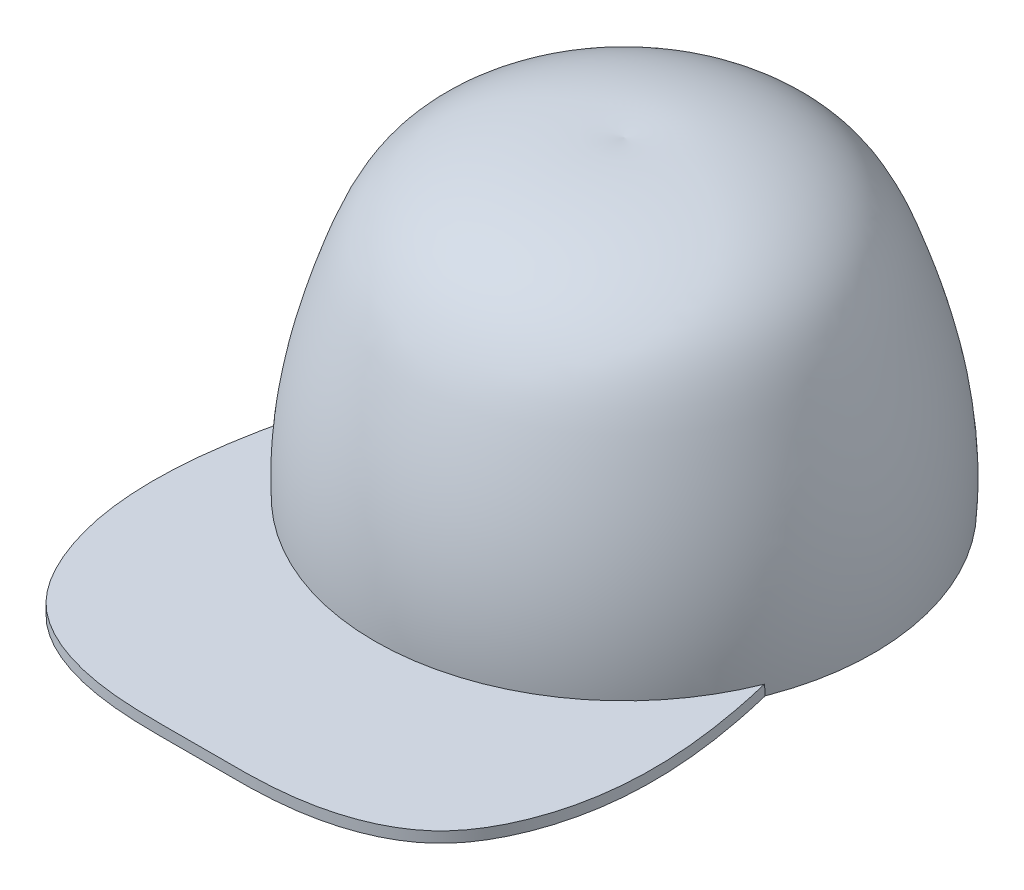
SolidWorks part; units mm, degrees
ref_plane "Front Plane" through (0, 0, 0) normal (0, 0, 1) x (1, 0, 0)
ref_plane "Top Plane" through (0, 0, 0) normal (0, 1, 0) x (1, 0, 0)
ref_plane "Right Plane" through (0, 0, 0) normal (1, 0, 0) x (0, 0, -1)
sketch "Sketch1" plane through (0, 0, 0) normal (0, 1, 0) x (1, 0, 0)
  line L0 (0, 0) -> (0, 270.85) construction
  line L1 (-90, 130.85) -> (90, 130.85) construction
  line L2 (96.5, 69.5) -> (0, 69.5) construction
  line L3 (76.5, 69.5) -> (76.5, 18.2) construction
  line L4 (36.5, 69.5) -> (36.5, 1.15) construction
  line L5 (70, 130.85) -> (70, 253.35) construction
  arc A0 (-90, 130.85) -> (90, 130.85) centre (0, 166.1897) ccw
  spline S0 degree 3 poles (90, 130.85) (96.9541, 101.6263) (102.4332, 59.8939) (68.9073, -0.1393) (23.6203, -1.1191) (0, 0) knots 0 0 0 0 0.464756 0.594997 1 1 1 1
  spline S1 degree 3 poles (-90, 130.85) (-96.9541, 101.6263) (-102.4332, 59.8939) (-68.9073, -0.1393) (-23.6203, -1.1191) (0, 0) knots 0 0 0 0 0.464756 0.594997 1 1 1 1
  spline S2 degree 2 poles (90, 130.85) (124.3948, 273.9038) (0, 270.85) knots 0 0 0 1 1 1
  spline S3 degree 2 poles (-90, 130.85) (-124.3948, 273.9038) (0, 270.85) knots 0 0 0 1 1 1
  point P3 (0, 69.5)
  point P4 (0, 130.85)
  point P7 (96.5, 69.5)
  point P8 (-96.5, 69.5)
  point P10 (90, 40.1)
  dimension "D1" = 69.5
  dimension "D2" = 130.85
  dimension "D3" = 90
  dimension "D4" = 122.5
  dimension "D5" = 140
  dimension "D6" = 96.5
  dimension "D7" = 96.5
  dimension "D8" = 90.75
  dimension "D9" = 20
  dimension "D10" = 51.3
  dimension "D11" = 60
  dimension "D12" = 68.35
  dimension "D13" = 69.5
  dimension "D14" = 20
sketch "Sketch5" plane through (0, 0, 0) normal (0, 1, 0) x (1, 0, 0)
  line L0 (0, 0) -> (0, 270.85) construction
  arc A0 (-90, 130.85) -> (90, 130.85) centre (0, 166.1715) ccw
  arc A1 (-88.1698, 131.6565) -> (88.2862, 131.881) centre (0.0144, 166.1955) ccw
  spline S0 degree 3 poles (-90, 130.85) (-97.0793, 101.6758) (-102.3198, 59.8491) (-75.2209, 11.0048) (-38.5303, -1.0698) (0, 0.4883) (38.5303, -1.0698) (75.2209, 11.0048) (102.3198, 59.8491) (97.0793, 101.6758) (90, 130.85) knots 0 0 0 0 0.232378 0.297499 0.407563 0.5 0.592437 0.702501 0.767622 1 1 1 1
  spline S1 degree 2 poles (-90, 130.85) (-124.3948, 273.9038) (0, 270.85) knots 0 0 0 1 1 1
  spline S2 degree 2 poles (-88.1698, 131.6565) (-122.168, 272.0844) (0, 268.85) knots 0 0 0 1 1 1
  spline S3 degree 2 poles (88.1698, 131.6565) (122.168, 272.0844) (0, 268.85) knots 0 0 0 1 1 1
  spline S4 degree 2 poles (90, 130.85) (124.3948, 273.9038) (0, 270.85) knots 0 0 0 1 1 1
  point P0 (-90, 130.85)
  point P1 (-96.5, 69.5)
  point P3 (-90, 40.1)
  point P5 (-76.5, 18.2)
  point P7 (-36.5, 1.15)
  point P9 (0, 0)
  point P11 (36.5, 1.15)
  point P13 (76.5, 18.2)
  point P15 (90, 40.1)
  point P17 (96.5, 69.5)
  point P19 (90, 130.85)
  point P21 (0, 69.5)
  point P28 (-70, 253.35)
  point P30 (-90, 130.85)
  point P32 (0, 270.85)
  point P34 (70, 253.35)
  point P36 (0, 268.85)
  point P38 (-68.7759, 251.7684)
  point P40 (68.4813, 252.0487)
  point P42 (88.2862, 131.881)
  point P44 (-88.1698, 131.6565)
  point P45 (0, 71.5)
  dimension "D1" = 2
  dimension "D2" = 2
  dimension "D3" = 2
  dimension "D4" = 2
  dimension "D5" = 2
  dimension "D6" = 2
sketch "Sketch7" plane through (0, 0, 0) normal (0, 1, 0) x (1, 0, 0)
  arc A0 (90, 130.85) -> (-90, 130.85) centre (0, 166.1767) cw
  spline S0 degree 3 poles (90, 130.85) (97.0793, 101.6758) (102.3198, 59.8491) (75.2209, 11.0048) (38.5303, -1.0698) (0, 0.4883) (-38.5303, -1.0698) (-75.2209, 11.0048) (-102.3198, 59.8491) (-97.0793, 101.6758) (-90, 130.85) knots 0 0 0 0 0.232378 0.297499 0.407563 0.5 0.592437 0.702501 0.767622 1 1 1 1
  point P0 (0, 0)
  point P1 (-36.5, 1.15)
  point P3 (-76.5, 18.2)
  point P5 (-90, 40.1)
  point P7 (-96.5, 69.5)
  point P9 (-90, 130.85)
  point P11 (0, 69.5)
  point P13 (90, 130.85)
  point P15 (96.5, 69.5)
  point P17 (90, 40.1)
  point P19 (76.5, 18.2)
  point P21 (36.5, 1.15)
extrude "Boss-Extrude3" add sketch "Sketch7" along normal blind 4.18
sketch "Sketch8" plane through (0, 0, 0) normal (0, -1, 0) x (-1, 0, 0)
  line L0 (0, 270.85) -> (0, -32.2535) construction
  arc A0 (88.1698, 131.6565) -> (-88.1698, 131.6565) centre (0, 166.4634) cw
  arc A1 (90, 130.85) -> (-90, 130.85) centre (0, 166.1503) cw
  spline S0 degree 2 poles (90, 130.85) (124.3948, 273.9038) (0, 270.85) knots 0 0 0 1 1 1
  spline S1 degree 2 poles (88.1698, 131.6565) (122.168, 272.0844) (0, 268.85) knots 0 0 0 1 1 1
  spline S2 degree 2 poles (-88.1698, 131.6565) (-122.168, 272.0844) (0, 268.85) knots 0 0 0 1 1 1
  spline S3 degree 2 poles (-90, 130.85) (-124.3948, 273.9038) (0, 270.85) knots 0 0 0 1 1 1
  point P0 (90, 130.85)
  point P1 (0, 69.5)
  point P3 (-90, 130.85)
  point P5 (-70, 253.35)
  point P7 (0, 270.85)
  point P9 (70, 253.35)
  point P11 (68.7759, 251.7684)
  point P13 (0, 268.85)
  point P15 (-68.4813, 252.0487)
  point P17 (-88.2862, 131.881)
  point P19 (0, 71.5)
  point P21 (88.1698, 131.6565)
sketch "Sketch9" plane through (0, 0, 0) normal (1, 0, 0) x (0, 0, -1)
  line L0 (0, 0) -> (270.85, 0) construction
  line L1 (166.18, 0) -> (166.18, 125) construction
  line L2 (166.18, 125) -> (166.18, 0)
  line L3 (166.18, 0) -> (69.5, 0)
  line L4 (166.18, 0) -> (166.18, 87.121) construction
  line L5 (166.18, 87.121) -> (166.18, 0)
  spline S0 degree 3 poles (69.5, 0) (67.5819, 26.8507) (75.089, 61.0707) (98.2638, 120.3419) (143.4984, 127.7419) (166.18, 125) knots 0 0 0 0 0.425687 0.582159 1 1 1 1
  spline S1 degree 3 poles (71.5, 0) (69.4865, 26.9773) (77.2565, 60.8484) (99.6163, 119.8609) (144.9681, 124.9589) (166.18, 123) knots 0 0 0 0 0.43212 0.590958 1 1 1 1
  point P4 (69.5, 0)
  point P5 (166.18, 0)
  point P10 (71.5, 0)
  point P12 (73.6015, 38.858)
  point P14 (83.7603, 77.0479)
  point P16 (96.5765, 102.8728)
  point P17 (124.9144, 119.4391)
  point P18 (166.18, 123)
  dimension "D1" = 69.5
  dimension "D2" = 96.68
  dimension "D3" = 125
  dimension "D4" = 2
  dimension "D5" = 2
  dimension "D6" = 2
  dimension "D7" = 2
  dimension "D8" = 2
  dimension "D9" = 2
sketch "Sketch10" plane through (0, 0, 0) normal (0, -1, 0) x (-1, 0, 0)
  line L0 (0, 69.5) -> (0, 270.85) construction
  arc A0 (-90, 130.85) -> (90, 130.85) centre (0, 166.0273) ccw
  spline S0 degree 2 poles (-90, 130.85) (-124.3948, 273.9038) (0, 270.85) knots 0 0 0 1 1 1
  spline S1 degree 2 poles (90, 130.85) (124.3948, 273.9038) (0, 270.85) knots 0 0 0 1 1 1
  point P0 (0, 69.5)
  point P1 (90, 130.85)
  point P3 (70, 253.35)
  point P5 (0, 270.85)
  point P7 (-70, 253.35)
  point P9 (-90, 130.85)
revolve "Revolve2" add sketch "Sketch9" angle 360 about L2
sketch "Sketch14" plane through (0, 4.18, 0) normal (0, 1, 0) x (1, 0, 0)
  line L0 (0, 0) -> (0, 69.26) construction
  arc A0 (-90.0956, 130.4551) -> (90.0956, 130.4551) centre (0, 166.18) ccw construction
  point P6 (0, 34.63)
sketch "Sketch15" plane through (0, 0, 0) normal (0, -1, 0) x (1, 0, 0)
  line L1 (26.3774, 283.3728) -> (453.0441, 283.3728) construction
